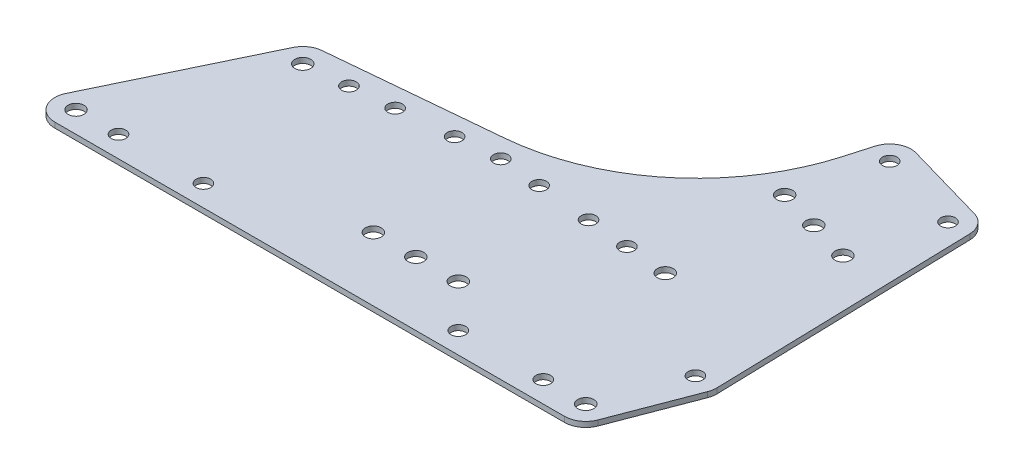
SolidWorks part; units mm, degrees
ref_plane "Front Plane" through (0, 0, 0) normal (0, 0, 1) x (1, 0, 0)
ref_plane "Top Plane" through (0, 0, 0) normal (0, 1, 0) x (1, 0, 0)
ref_plane "Right Plane" through (0, 0, 0) normal (1, 0, 0) x (0, 0, -1)
sketch "Sketch1" plane through (0, 0, 0) normal (0, 1, 0) x (1, 0, 0)
  line L0 (76.2, 50.8) -> (22.002, 45.7881) construction
  line L1 (76.2, 50.8) -> (130.398, 45.7881) construction
  line L2 (152.4, 76.8932) -> (127.9822, 83.8881) construction
  line L3 (127.9822, 83.8881) -> (134.9771, 108.306) construction
  line L4 (152.4, 76.8932) -> (159.395, 101.311) construction
  line L5 (76.2, 12.7) -> (101.6, 12.7) construction
  line L6 (0, -6.35) -> (152.4, -6.35)
  line L7 (158.3321, -2.2655) -> (167.3942, 21.4629)
  line L8 (167.8099, 23.8976) -> (165.7427, 101.4801)
  line L10 (128.8727, 110.0547) -> (126.7045, 102.4859)
  line L11 (71.507, 56.7431) -> (21.4173, 52.1112)
  line L12 (16.2785, 48.5384) -> (-5.7235, 2.7502)
  line L13 (136.7259, 114.4104) -> (161.1437, 107.4154)
  circle A0 centre (0, 0) radius 2.3813
  circle A1 centre (22.002, 45.7881) radius 2.3813
  circle A2 centre (76.2, 12.7) radius 2.3813
  circle A3 centre (130.398, 45.7881) radius 2.3813
  circle A4 centre (152.4, 0) radius 2.3813
  circle A5 centre (76.2, 50.8) radius 2.1828
  circle A6 centre (63.554, 49.6306) radius 2.1828
  circle A7 centre (88.846, 49.6306) radius 2.1828
  circle A8 centre (117.752, 46.9576) radius 2.1828
  circle A9 centre (105.1059, 48.127) radius 2.1828
  circle A10 centre (34.648, 46.9576) radius 2.1828
  circle A11 centre (47.2941, 48.127) radius 2.1828
  circle A12 centre (152.4, 76.8932) radius 2.3813
  circle A13 centre (127.9822, 83.8881) radius 2.3813
  circle A14 centre (140.1911, 80.3906) radius 2.3813
  circle A15 centre (134.9771, 108.306) radius 2.1828
  circle A16 centre (159.395, 101.311) radius 2.1828
  circle A17 centre (161.4621, 23.7284) radius 2.1828
  circle A18 centre (12.7, 0) radius 2.1828
  circle A19 centre (38.1, 0) radius 2.1828
  circle A20 centre (101.6, 12.7) radius 2.3813
  circle A21 centre (88.9, 12.7) radius 2.3813
  circle A22 centre (139.7, 0) radius 2.1828
  circle A23 centre (114.3, 0) radius 2.1828
  arc A24 (126.7045, 102.4859) -> (71.507, 56.7431) centre (65.6599, 119.9733) cw
  arc A25 (21.4173, 52.1112) -> (16.2785, 48.5384) centre (22.002, 45.7881) ccw
  arc A26 (-5.7235, 2.7502) -> (0, -6.35) centre (0, 0) ccw
  arc A27 (158.3321, -2.2655) -> (152.4, -6.35) centre (152.4, 0) cw
  arc A28 (167.3942, 21.4629) -> (167.8099, 23.8976) centre (161.4621, 23.7284) ccw
  arc A29 (165.7427, 101.4801) -> (161.1437, 107.4154) centre (159.395, 101.311) ccw
  arc A30 (136.7259, 114.4104) -> (128.8727, 110.0547) centre (134.9771, 108.306) ccw
  point P70 (36.9247, 9.3901)
  point P71 (8.8708, 9.0884)
  point P72 (143.7982, 9.3434)
  point P73 (115.8752, 10.8419)
  dimension "D9" = 4.7625
  dimension "D10" = 4.7625
  dimension "D11" = 4.7625
  dimension "D12" = 4.7625
  dimension "D13" = 4.7625
  dimension "D15" = 4.3656
  dimension "D19" = 4.3656
  dimension "D20" = 4.3656
  dimension "D23" = 4.3656
  dimension "D24" = 4.3656
  dimension "D27" = 4.3656
  dimension "D28" = 4.3656
  dimension "D31" = 4.7625
  dimension "D32" = 4.7625
  dimension "D33" = 4.7625
  dimension "D40" = 4.3656
  dimension "D41" = 4.3656
  dimension "D44" = 4.3656
  dimension "D45" = 4.3656
  dimension "D48" = 4.3656
  dimension "D50" = 4.7625
  dimension "D51" = 4.7625
  dimension "D54" = 4.3656
  dimension "D55" = 4.3656
  dimension "D69" = 63.5
  dimension "D70" = 6.35
  dimension "D1" = 50.8
  dimension "D2" = 63.5
  dimension "D3" = 63.5
  dimension "D4" = 50.8
  dimension "D5" = 12.7
  dimension "D6" = 12.7
  dimension "D7" = 76.2
  dimension "D8" = 76.2
  dimension "D14" = 38.1
  dimension "D16" = 76.2
  dimension "D17" = 12.7
  dimension "D18" = 12.7
  dimension "D21" = 25.4
  dimension "D22" = 12.7
  dimension "D25" = 25.4
  dimension "D26" = 12.7
  dimension "D29" = 38.1
  dimension "D30" = 25.4
  dimension "D34" = 38.1
  dimension "D35" = 0
  dimension "D36" = 25.4
  dimension "D37" = 90
  dimension "D38" = 25.4
  dimension "D39" = 90
  dimension "D42" = 25.4
  dimension "D43" = 38.1
  dimension "D46" = 12.7
  dimension "D47" = 38.1
  dimension "D49" = 25.4
  dimension "D52" = 12.7
  dimension "D53" = 38.1
  dimension "D56" = 6.35
  dimension "D57" = 6.35
  dimension "D58" = 6.35
  dimension "D59" = 6.35
  dimension "D60" = 6.35
  dimension "D61" = 6.35
  dimension "D62" = 6.35
  dimension "D63" = 6.35
  dimension "D64" = 6.35
  dimension "D65" = 6.35
  dimension "D66" = 6.35
  dimension "D67" = 6.35
  dimension "D68" = 6.35
  dimension "D71" = 0
  dimension "D72" = 0
  dimension "D73" = 0
  dimension "D74" = 0
extrude "Boss-Extrude1" add sketch "Sketch1" along normal blind 1.5875
